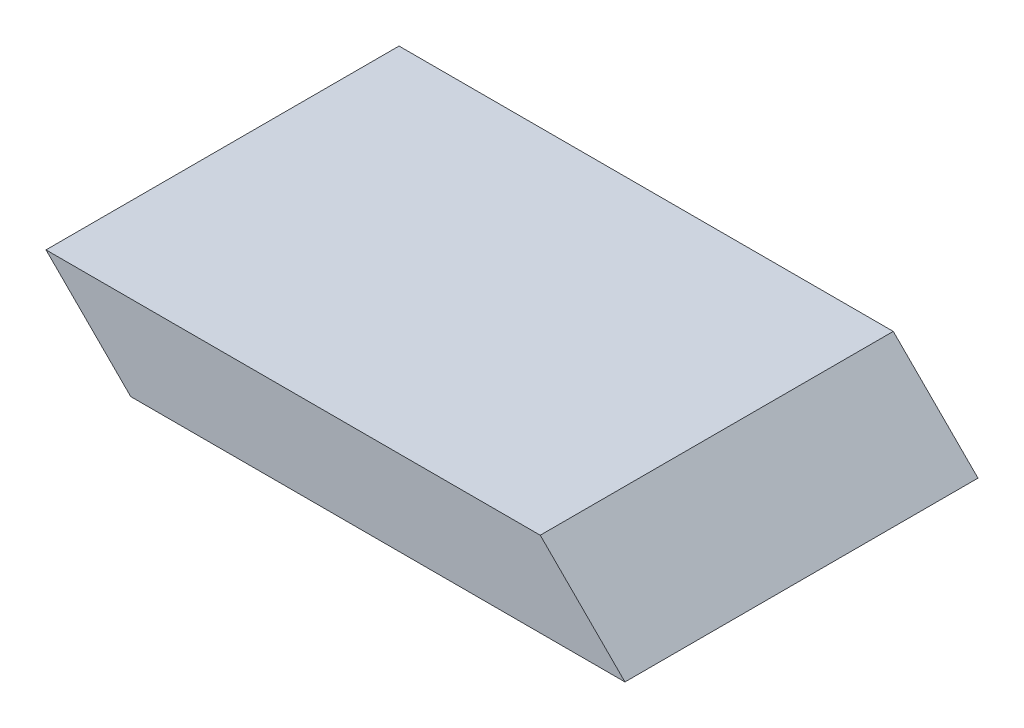
SolidWorks part; units mm, degrees
ref_plane "Front Plane" through (0, 0, 0) normal (0, 0, 1) x (1, 0, 0)
ref_plane "Top Plane" through (0, 0, 0) normal (0, 1, 0) x (1, 0, 0)
ref_plane "Right Plane" through (0, 0, 0) normal (1, 0, 0) x (0, 0, -1)
sketch "Sketch1" plane through (0, 0, 0) normal (0, 1, 0) x (1, 0, 0)
  line L1 (-44.45, 31.75) -> (44.45, 31.75)
  line L2 (-44.45, 31.75) -> (-44.45, -31.75)
  line L3 (-44.45, -31.75) -> (44.45, -31.75)
  line L4 (44.45, 31.75) -> (44.45, -31.75)
  line L5 (-44.45, 31.75) -> (44.45, -31.75) construction
  line L6 (-44.45, -31.75) -> (44.45, 31.75) construction
  point P0 (0, 0)
  dimension "D1" = 88.9
  dimension "D2" = 63.5
extrude "Boss-Extrude1" add sketch "Sketch1" along normal blind 15.24
sketch "Sketch2" plane through (0, 0, 31.75) normal (0, 0, 1) x (1, 0, 0)
  line L0 (44.45, 15.24) -> (59.69, 0)
  line L1 (59.69, 0) -> (44.45, 0)
  line L2 (44.45, 15.24) -> (44.45, 0)
  dimension "D1" = 45
extrude "Boss-Extrude2" add sketch "Sketch2" against normal up to surface (63.5 mm away) up to face at (0, 7.62, -31.75)
sketch "Sketch3" plane through (0, 0, -31.75) normal (0, 0, -1) x (-1, 0, 0)
  line L0 (44.45, 15.24) -> (29.21, 0)
  line L1 (-59.69, 0) -> (44.45, 0) construction
  line L2 (29.21, 0) -> (44.45, 0)
  line L3 (44.45, 0) -> (44.45, 15.24)
  dimension "D1" = 45
extrude "Cut-Extrude1" cut sketch "Sketch3" against normal up to surface (63.5 mm away) up to face at (3.81, 7.62, 31.75)
